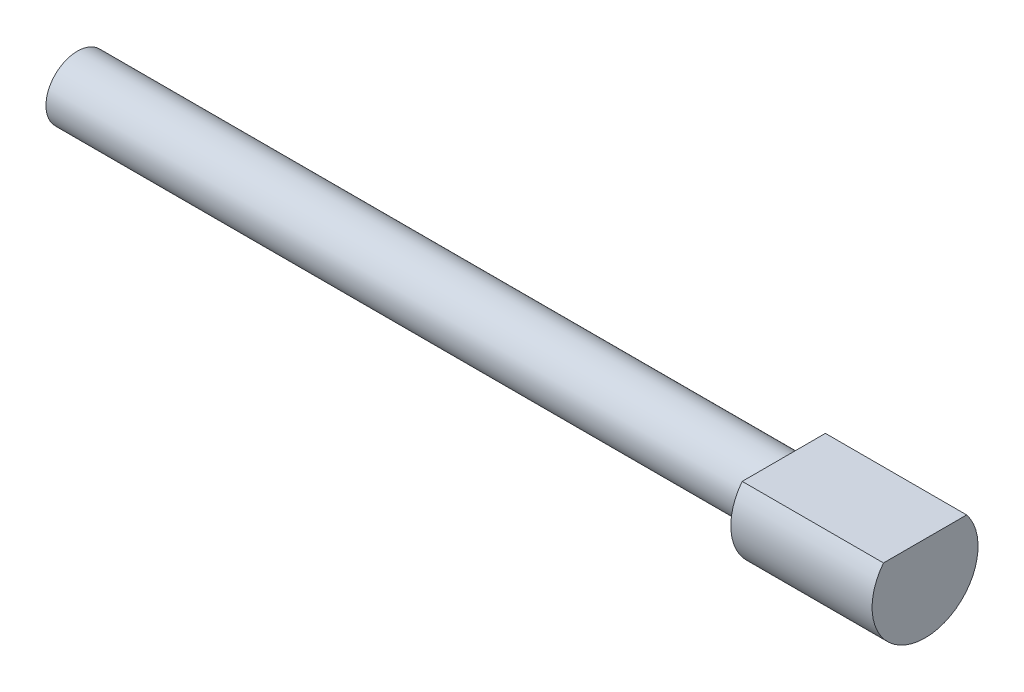
SolidWorks part; units mm, degrees
material "AISI 304"
ref_plane "Front Plane" through (0, 0, 0) normal (0, 0, 1) x (1, 0, 0)
ref_plane "Top Plane" through (0, 0, 0) normal (0, 1, 0) x (1, 0, 0)
ref_plane "Right Plane" through (0, 0, 0) normal (1, 0, 0) x (0, 0, -1)
sketch "Sketch2" plane through (0, 0, 0) normal (1, 0, 0) x (0, 0, -1)
  circle A0 centre (0, 0) radius 1.1303
  dimension "D1" = 2.2606
extrude "Boss-Extrude1" add sketch "Sketch2" against normal blind 25.4
sketch "Sketch3" plane through (0, 0, 0) normal (1, 0, 0) x (0, 0, -1)
  circle A0 centre (0, 0) radius 1.905
  dimension "D1" = 3.81
extrude "Boss-Extrude2" add sketch "Sketch3" along normal blind 5.08
sketch "Sketch4" plane through (5.08, 0, 0) normal (1, 0, 0) x (0, 0, -1)
  line L0 (-1.4954, 1.1802) -> (1.4954, 1.1802)
  circle A0 centre (0, 0) radius 1.905 construction
  arc A1 (-1.4954, 1.1802) -> (1.4954, 1.1802) centre (0, 0) cw
  circle M1 centre (0, 0) radius 1.905
extrude "Cut-Extrude1" cut sketch "Sketch4" against normal blind 5.08 contours L0 M1
